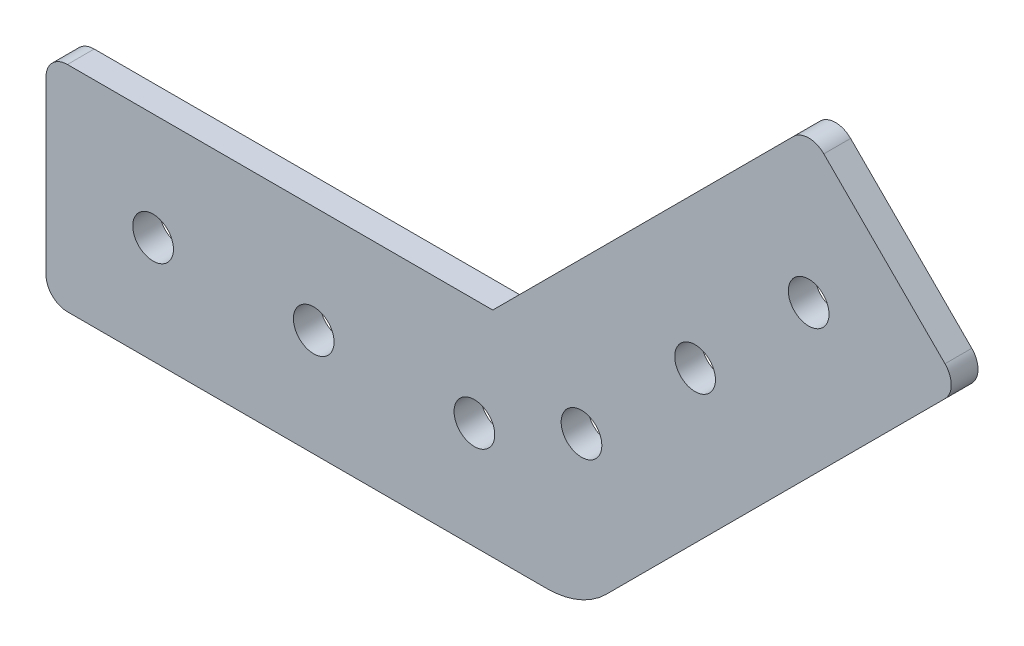
SolidWorks part; units mm, degrees
ref_plane "Front Plane" through (0, 0, 0) normal (0, 0, 1) x (1, 0, 0)
ref_plane "Top Plane" through (0, 0, 0) normal (0, 1, 0) x (1, 0, 0)
ref_plane "Right Plane" through (0, 0, 0) normal (1, 0, 0) x (0, 0, -1)
sketch "Sketch1" plane through (0, 0, 0) normal (0, 0, 1) x (1, 0, 0)
  line L0 (0, 0) -> (63.5, 0)
  line L1 (63.5, 0) -> (108.4013, 44.9013)
  line L2 (108.4013, 44.9013) -> (90.4408, 62.8618)
  line L3 (90.4408, 62.8618) -> (52.979, 25.4)
  line L4 (52.979, 25.4) -> (0, 25.4)
  line L5 (0, 25.4) -> (0, 0)
  line L6 (52.979, 25.4) -> (63.5, 0) construction
  line L7 (0, 12.7) -> (76.2, 12.7) construction
  line L8 (99.421, 53.8815) -> (45.5395, 0) construction
  circle A0 centre (12.7, 12.7) radius 2.413
  circle A1 centre (31.75, 12.7) radius 2.413
  circle A2 centre (76.9704, 31.4309) radius 2.413
  circle A3 centre (90.4408, 44.9013) radius 2.413
  circle A4 centre (50.8, 12.7) radius 2.413
  circle A5 centre (63.5, 17.9605) radius 2.413
  dimension "D6" = 4.826
  dimension "D7" = 4.826
  dimension "D8" = 4.826
  dimension "D9" = 4.826
  dimension "D14" = 4.826
  dimension "D15" = 4.826
  dimension "D17" = 19.05
  dimension "D1" = 135
  dimension "D2" = 25.4
  dimension "D3" = 25.4
  dimension "D4" = 63.5
  dimension "D5" = 63.5
  dimension "D10" = 12.7
  dimension "D11" = 19.05
  dimension "D12" = 12.7
  dimension "D13" = 19.05
  dimension "D16" = 19.05
extrude "Boss-Extrude1" add sketch "Sketch1" along normal blind 3.175
fillet "Fillet1" radius 10 1 edges at (63.5, 0, 1.5875)
fillet "Fillet2" radius 2.54 1 edges at (0, 25.4, 1.5875)
fillet "Fillet3" radius 2.54 3 edges at (90.4408, 62.8618, 1.5875) (108.4013, 44.9013, 1.5875) (0, 0, 1.5875)
